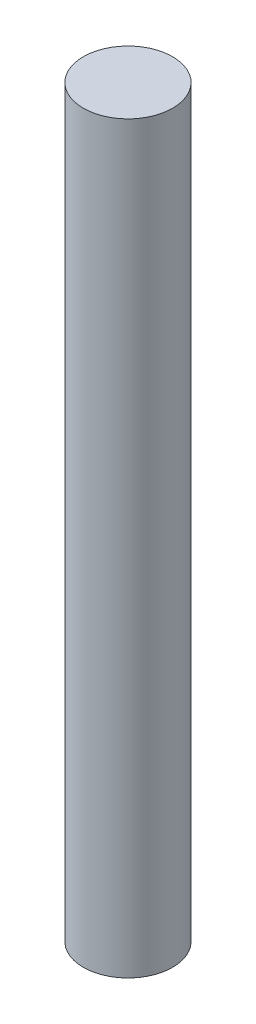
SolidWorks part; units mm, degrees
ref_plane "Front Plane" through (0, 0, 0) normal (0, 0, 1) x (1, 0, 0)
ref_plane "Top Plane" through (0, 0, 0) normal (0, 1, 0) x (1, 0, 0)
ref_plane "Right Plane" through (0, 0, 0) normal (1, 0, 0) x (0, 0, -1)
sketch "Sketch2" plane through (0, 0, 0) normal (0, 1, 0) x (1, 0, 0)
  circle A0 centre (0, 0) radius 1.8
  dimension "D1" = 3.6
extrude "Boss-Extrude1" add sketch "Sketch2" along normal blind 30
